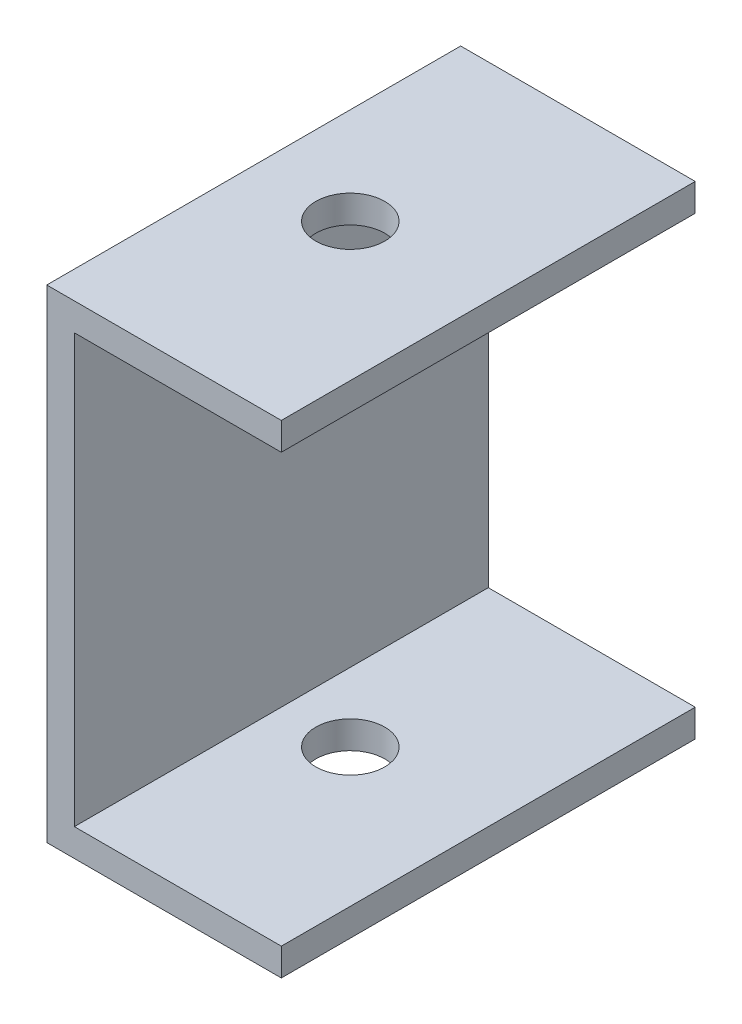
SolidWorks part; units mm, degrees
ref_plane "Front Plane" through (0, 0, 0) normal (0, 0, 1) x (1, 0, 0)
ref_plane "Top Plane" through (0, 0, 0) normal (0, 1, 0) x (1, 0, 0)
ref_plane "Right Plane" through (0, 0, 0) normal (1, 0, 0) x (0, 0, -1)
sketch "Sketch1" plane through (0, 0, 0) normal (0, 0, 1) x (1, 0, 0)
  line L0 (0, 0) -> (0, 28)
  line L1 (0, 28) -> (2, 28)
  line L2 (2, 28) -> (2, 2)
  line L3 (2, 2) -> (17, 2)
  line L4 (17, 2) -> (17, 0)
  line L5 (17, 0) -> (0, 0)
  dimension "D1" = 2
  dimension "D2" = 2
  dimension "D3" = 15
  dimension "D4" = 26
extrude "Boss-Extrude1" add sketch "Sketch1" along normal blind 30
sketch "Sketch2" plane through (0, 2, 0) normal (0, 1, 0) x (1, 0, 0)
  line L0 (2, -30) -> (2, 0) construction
  line L1 (17, 0) -> (2, 0) construction
  circle A0 centre (7, -15) radius 2.5
  dimension "D1" = 5
  dimension "D2" = 15
extrude "Cut-Extrude1" cut sketch "Sketch2" against normal blind 10
sketch "Sketch3" plane through (2, 0, 0) normal (1, 0, 0) x (0, 0, -1)
  line L0 (-30, 28) -> (0, 28) construction
  line L1 (-30, 2) -> (-30, 28) construction
  circle A0 centre (-15, 23) radius 2.5
  dimension "D1" = 5
  dimension "D2" = 15
extrude "Cut-Extrude2" cut sketch "Sketch3" against normal blind 10
sketch "Sketch4" plane through (0, 28, 0) normal (0, 1, 0) x (1, 0, 0)
  line L0 (2, -30) -> (0, -30) construction
  line L1 (0, 0) -> (2, 0)
  line L2 (0, 0) -> (0, -30)
  line L3 (0, -30) -> (2, -30)
  line L4 (2, 0) -> (2, -30)
  line L5 (0, 0) -> (2, -30) construction
  line L6 (0, -30) -> (2, 0) construction
  point P0 (1, -15)
  point P5 (2, 0)
  point P7 (0, 0)
  point P8 (0, 0)
  point P10 (2, -30)
extrude "Boss-Extrude2" add sketch "Sketch4" along normal blind 5
sketch "Sketch5" plane through (0, 33, 0) normal (0, 1, 0) x (1, 0, 0)
  line L1 (17, 0) -> (0, 0)
  line L2 (17, 0) -> (17, -30)
  line L3 (17, -30) -> (0, -30)
  line L4 (0, 0) -> (0, -30)
  line L5 (17, 0) -> (0, -30) construction
  line L6 (17, -30) -> (0, 0) construction
  point P0 (8.5, -15)
  point P6 (0, 0)
  dimension "D1" = 17
extrude "Boss-Extrude3" add sketch "Sketch5" along normal blind 2
sketch "Sketch6" plane through (0, 33, 0) normal (0, -1, 0) x (1, 0, 0)
  line L0 (2, 30) -> (2, 0) construction
  circle A0 centre (7, 15) radius 2.5
  dimension "D1" = 5
extrude "Cut-Extrude3" cut sketch "Sketch6" against normal blind 2
